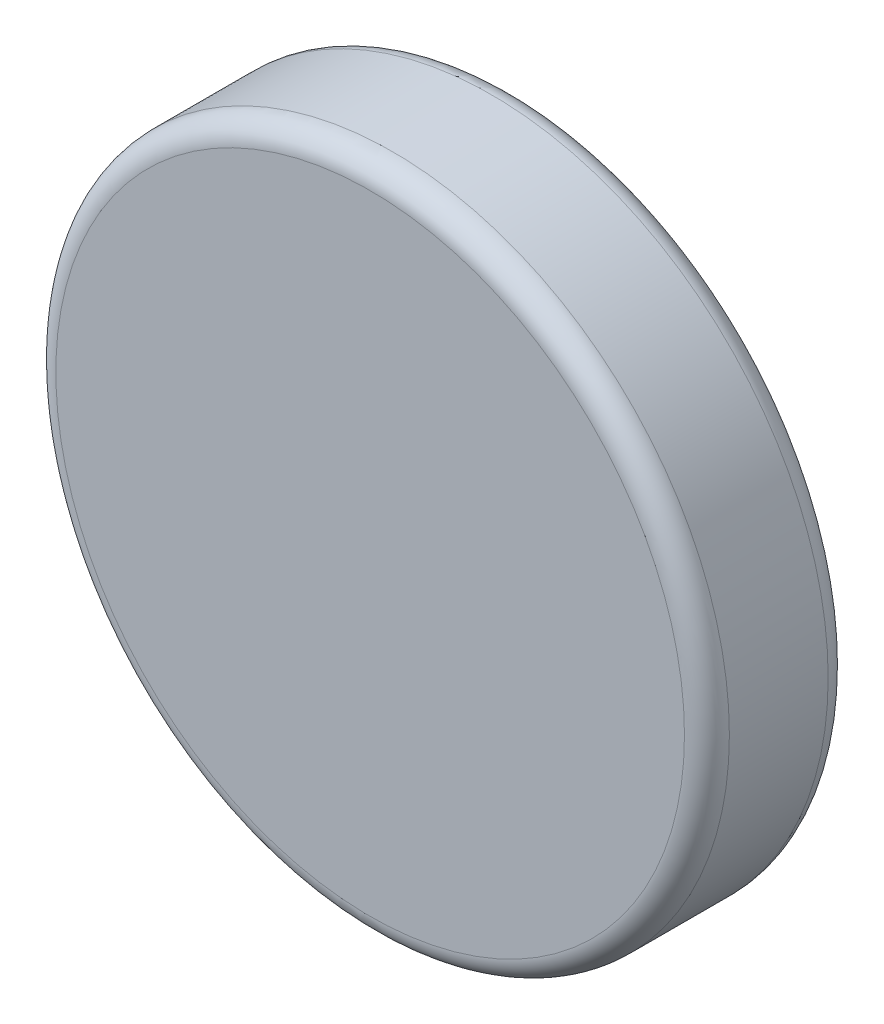
SolidWorks part; units mm, degrees
ref_plane "Front Plane" through (0, 0, 0) normal (0, 0, 1) x (1, 0, 0)
ref_plane "Top Plane" through (0, 0, 0) normal (0, 1, 0) x (1, 0, 0)
ref_plane "Right Plane" through (0, 0, 0) normal (1, 0, 0) x (0, 0, -1)
sketch "Sketch1" plane through (0, 0, 0) normal (0, 0, 1) x (1, 0, 0)
  circle A0 centre (0, 0) radius 7.5
  dimension "D1" = 15
extrude "Boss-Extrude1" add sketch "Sketch1" along normal blind 3.2
fillet "Fillet1" radius 0.5 2 edges at (7.5, 0, 0) (7.5, 0, 3.2)
